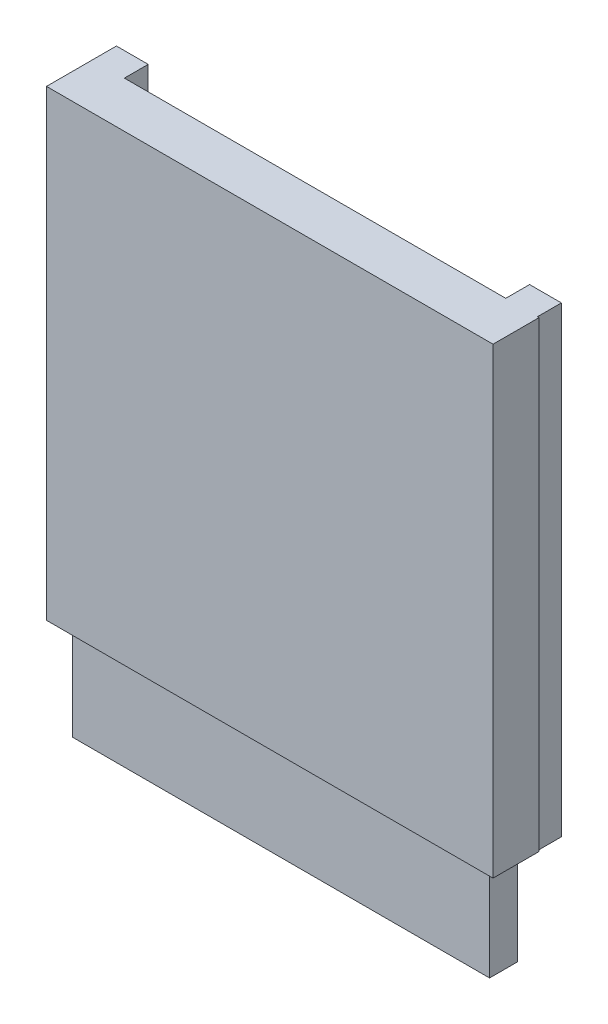
SolidWorks part; units mm, degrees
ref_plane "Front" through (0, 0, 0) normal (0, 0, 1) x (1, 0, 0)
ref_plane "Top" through (0, 0, 0) normal (0, 1, 0) x (1, 0, 0)
ref_plane "Right" through (0, 0, 0) normal (1, 0, 0) x (0, 0, -1)
sketch "Sketch1" plane through (0, 0, 0) normal (0, 0, 1) x (1, 0, 0)
  circle A0 centre (0, 0) radius 0.5
  circle A1 centre (26, 0) radius 0.5
  dimension "D1" = 1
  dimension "D2" = 1
  dimension "D3" = 26
extrude "Extrude1" add sketch "Sketch1" against normal blind 0.508
sketch "Sketch2" plane through (0, 0, 0) normal (0, 0, 1) x (1, 0, 0)
  line L1 (-1, 2.8) -> (1, 2.8)
  line L2 (-1, 2.8) -> (-1, -26.3)
  line L3 (-1, -26.3) -> (1, -26.3)
  line L4 (1, 2.8) -> (1, -26.3)
  line L5 (25, 2.8) -> (27, 2.8)
  line L6 (25, 2.8) -> (25, -26.3)
  line L7 (25, -26.3) -> (27, -26.3)
  line L8 (27, 2.8) -> (27, -26.3)
  circle A0 centre (26, 0) radius 0.5 construction
  dimension "D6" = 26.3
  dimension "D7" = 1
  dimension "D1" = 2
  dimension "D2" = 29.1
  dimension "D3" = 1
  dimension "D4" = 26.3
  dimension "D5" = 2
  dimension "D8" = 29.1
extrude "Extrude2" add sketch "Sketch2" along normal blind 1.5
sketch "Sketch3" plane through (0, 0, 1.5) normal (0, 0, 1) x (1, 0, 0)
  line L1 (-1, 2.8) -> (27.1, 2.8)
  line L2 (-1, 2.8) -> (-1, -26.3)
  line L3 (-1, -26.3) -> (27.1, -26.3)
  line L4 (27.1, 2.8) -> (27.1, -26.3)
  dimension "D1" = 28.1
  dimension "D2" = 29.1
extrude "Extrude3" add sketch "Sketch3" along normal blind 2.9
sketch "Sketch4" plane through (0, -26.3, 0) normal (0, -1, 0) x (1, 0, 0)
  line L1 (26.5755, 4.0316) -> (-0.5066, 4.0316)
  line L2 (26.5755, 4.0316) -> (26.5755, 1.7592)
  line L3 (26.5755, 1.7592) -> (-0.5066, 1.7592)
  line L4 (-0.5066, 4.0316) -> (-0.5066, 1.7592)
extrude "Cut-Extrude1" cut sketch "Sketch4" against normal blind 26.3
sketch "Sketch5" plane through (0, 0, 0) normal (0, -1, 0) x (1, 0, 0)
  line L0 (0, -0.508) -> (0, 0) construction
  line L1 (26.2331, 3.7515) -> (0, 3.7515)
  line L2 (26.2331, 3.7515) -> (26.2331, 2.0083)
  line L3 (26.2331, 2.0083) -> (0, 2.0083)
  line L4 (0, 3.7515) -> (0, 2.0083)
extrude "Extrude4" add sketch "Sketch5" along normal blind 32.5
